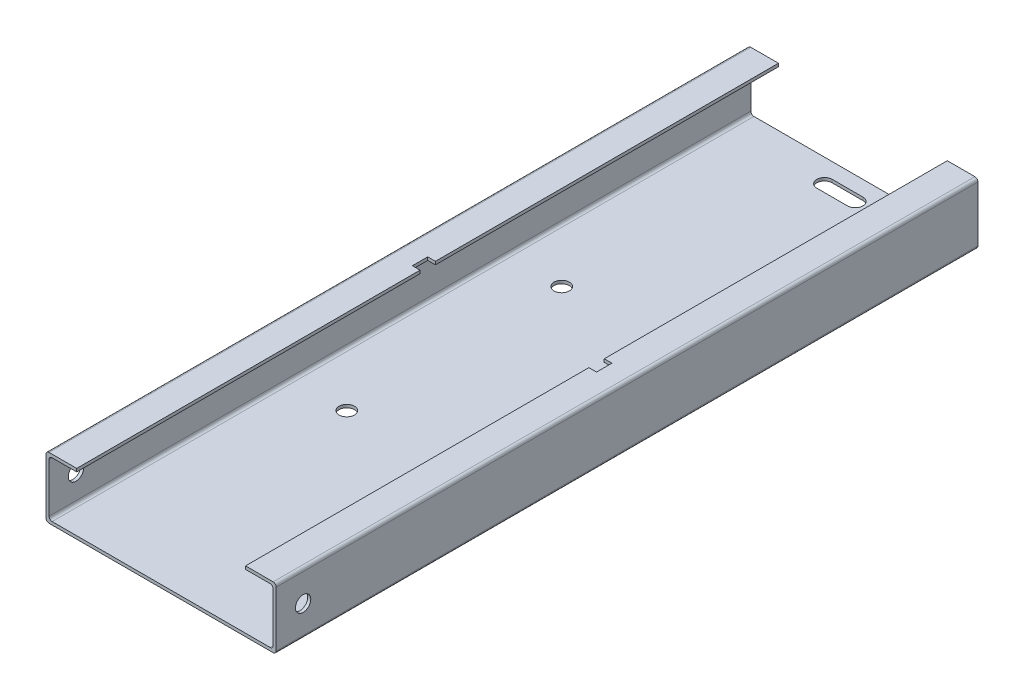
SolidWorks part; units mm, degrees
ref_plane "Alzado" through (0, 0, 0) normal (0, 0, 1) x (1, 0, 0)
ref_plane "Planta" through (0, 0, 0) normal (0, 1, 0) x (1, 0, 0)
ref_plane "Vista lateral" through (0, 0, 0) normal (1, 0, 0) x (0, 0, -1)
sketch "Croquis2" plane through (0, 0, 0) normal (0, 0, 1) x (1, 0, 0)
  line L0 (-75, 20) -> (-55, 20)
  line L1 (-75, -20) -> (75, -20)
  line L2 (-75, -20) -> (-75, 20)
  line L4 (75, -20) -> (75, 20)
  line L5 (-67.6394, -18.0372) -> (-67.5, -18) construction
  line L6 (75, 20) -> (55, 20)
  line L7 (-73, -18) -> (73, -18)
  line L8 (-73, -18) -> (-73, 18)
  line L10 (73, -18) -> (73, 18)
  line L11 (-73, -18) -> (-67.6394, -18.0372) construction
  line L12 (-55, 20) -> (-55, 18)
  line L13 (-55, 18) -> (-73, 18)
  line L14 (73, 18) -> (55, 18)
  line L15 (55, 18) -> (55, 20)
  point P0 (0, 0)
  point P6 (71.25, -19)
  dimension "D1" = 150
  dimension "D2" = 40
  dimension "D3" = 146
  dimension "D4" = 36
  dimension "D5" = 20
extrude "Saliente-Extruir2" add sketch "Croquis2" along normal mid plane 457.2
fillet "Redondeo1" radius 2 8 edges at (-73, 18, 0) (73, 18, 0) (-75, -20, 0) (75, -20, 0) (75, 20, 0) (73, -18, 0) (-73, -18, 0) (-75, 20, 0)
sketch "Croquis3" plane through (75, 0, 0) normal (1, 0, 0) x (0, 0, -1)
  line L0 (-228.6, -18) -> (-228.6, 18) construction
  line L1 (-228.6, -18) -> (228.6, -18) construction
  circle A0 centre (-211.1, 0) radius 5
  dimension "D1" = 10
  dimension "D2" = 17.5
  dimension "D3" = 18
extrude "Cortar-Extruir1" cut sketch "Croquis3" against normal through all
sketch "Croquis4" plane through (0, 20, 0) normal (0, 1, 0) x (1, 0, 0)
  line L0 (-55, -228.6) -> (-55, 228.6) construction
  line L1 (-55, 5.1) -> (-60, 5.1)
  line L2 (-55, 5.1) -> (-55, -4.9)
  line L3 (-55, -4.9) -> (-60, -4.9)
  line L4 (-60, 5.1) -> (-60, -4.9)
  line L5 (-55, 228.6) -> (-73, 228.6) construction
  line L6 (0, -22) -> (0, 22) construction
  line L7 (60, 5.1) -> (60, -4.9)
  line L8 (55, -4.9) -> (60, -4.9)
  line L9 (55, 5.1) -> (55, -4.9)
  line L10 (55, 5.1) -> (60, 5.1)
  dimension "D1" = 10
  dimension "D2" = 5
  dimension "D3" = 223.5
extrude "Cortar-Extruir2" cut sketch "Croquis4" against normal blind 10
sketch "Croquis5" plane through (0, -20, 0) normal (0, -1, 0) x (1, 0, 0)
  line L0 (-10, -213.6) -> (10, -213.6) construction
  line L1 (-10, -208.6) -> (10, -208.6)
  line L2 (-10, -218.6) -> (10, -218.6)
  line L3 (0, 0) -> (0, -245.0745) construction
  line L4 (-73, -228.6) -> (73, -228.6) construction
  line L5 (0, 0) -> (-75, 0) construction
  line L6 (-75, -228.6) -> (-75, 228.6) construction
  arc A0 (-10, -208.6) -> (-10, -218.6) centre (-10, -213.6) ccw
  arc A1 (10, -218.6) -> (10, -208.6) centre (10, -213.6) ccw
  circle A2 centre (-37.6442, -70) radius 5
  circle A3 centre (32.3558, -70) radius 5
  circle A4 centre (32.3558, 70) radius 5
  circle A5 centre (-37.6442, 70) radius 5
  point P2 (0, -213.6)
  dimension "D1" = 5
  dimension "D3" = 15
  dimension "D4" = 10
  dimension "D2" = 20
  dimension "D5" = 70
  dimension "D6" = 2
  dimension "D7" = 2
extrude "Cortar-Extruir3" cut sketch "Croquis5" against normal blind 10
